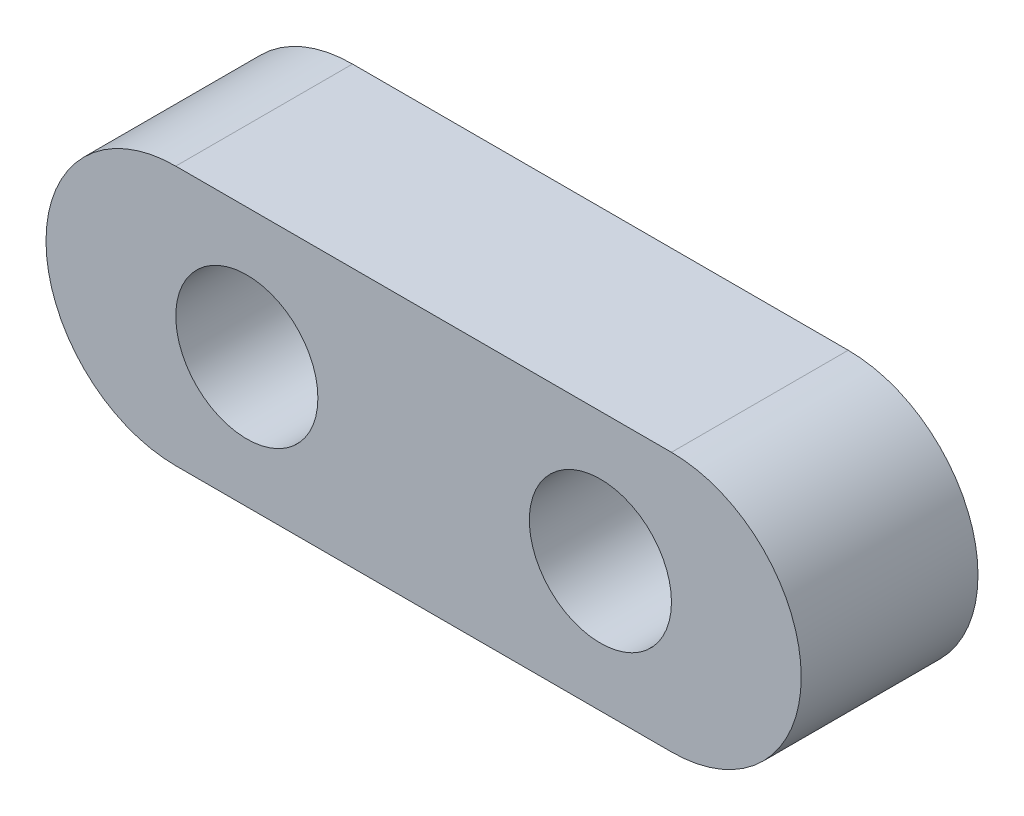
SolidWorks part; units mm, degrees
ref_plane "Front Plane" through (0, 0, 0) normal (0, 0, 1) x (1, 0, 0)
ref_plane "Top Plane" through (0, 0, 0) normal (0, 1, 0) x (1, 0, 0)
ref_plane "Right Plane" through (0, 0, 0) normal (1, 0, 0) x (0, 0, -1)
sketch "Sketch1" plane through (0, 0, 0) normal (0, 0, 1) x (1, 0, 0)
  line L0 (8.9027, 0) -> (-8.9027, 0) construction
  line L1 (8.9027, -4.6609) -> (-8.9027, -4.6609)
  line L2 (8.9027, 4.6609) -> (-8.9027, 4.6609)
  arc A0 (8.9027, -4.6609) -> (8.9027, 4.6609) centre (8.9027, 0) ccw
  arc A1 (-8.9027, 4.6609) -> (-8.9027, -4.6609) centre (-8.9027, 0) ccw
  point P2 (0, 0)
  dimension "D1" = 17.8054
  dimension "D2" = 9.3218
extrude "Boss-Extrude1" add sketch "Sketch1" along normal blind 6.35 contours L2 A1 L1 A0
hole_wizard "#10 Clearance Hole1" positions "Sketch2" profile "Sketch3" hole size "#10" standard "ANSI Inch" end condition through all
sketch "Sketch2" plane through (0, 0, 6.35) normal (0, 0, 1) x (1, 0, 0)
  line L1 (-6.35, 0) -> (6.35, 0) construction
  line L3 (8.9027, 4.6609) -> (-8.9027, 4.6609) construction
  line L4 (8.9027, -4.6609) -> (-8.9027, -4.6609) construction
  point P0 (-6.35, 0)
  point P2 (6.35, 0)
  point P11 (0, 0)
  point P14 (0, 4.6609)
  dimension "D1" = 12.7
  dimension "D2" = 4.6609
sketch "Sketch3" plane through (-6.35, 0, 6.35) normal (1, 0, 0) x (0, -1, 0)
  line L0 (0, 0) -> (0, 6.35)
  line L1 (0, 6.35) -> (2.5527, 6.35)
  line L2 (2.5527, 6.35) -> (2.5527, 0)
  line L5 (2.5527, 0) -> (0, 0)
  line L11 (0, -6.35) -> (0, 107.95) construction
  dimension "Thru Hole Dia." = 5.1054
  dimension "Thru Hole Depth" = 6.35
